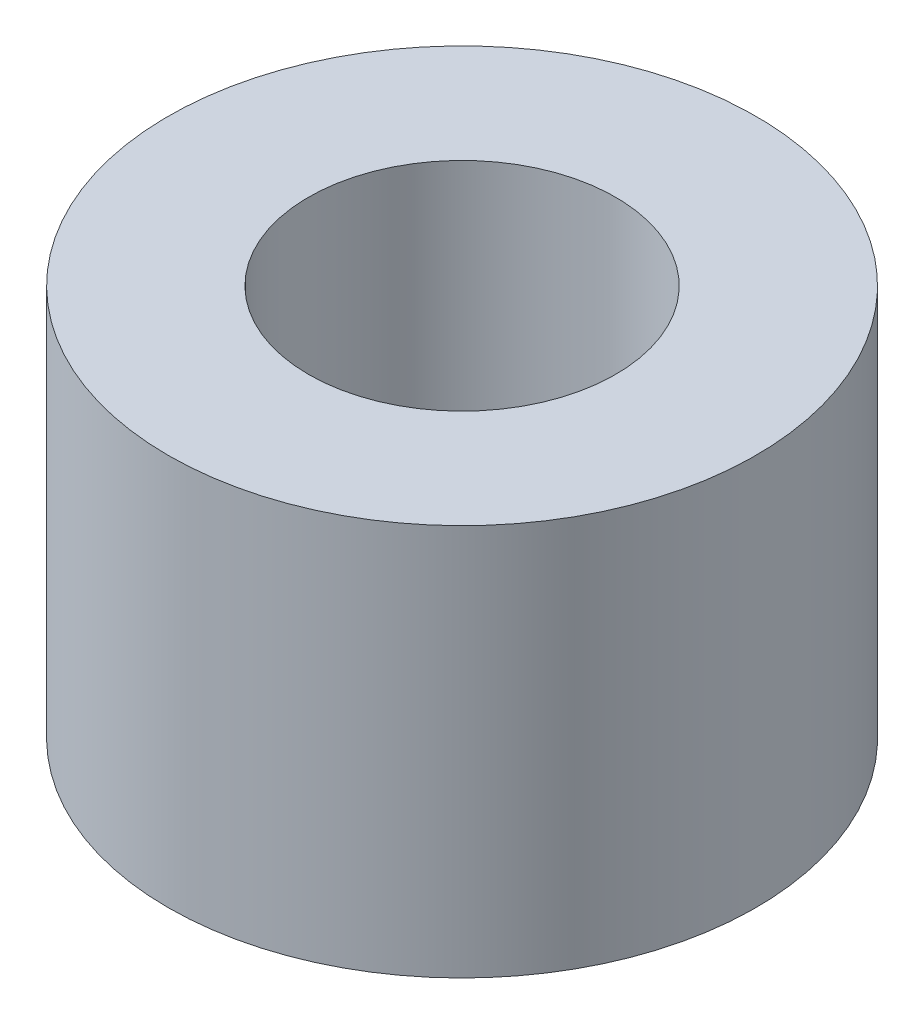
SolidWorks part; units mm, degrees
material "6061 Alloy"
ref_plane "Front Plane" through (0, 0, 0) normal (0, 0, 1) x (1, 0, 0)
ref_plane "Top Plane" through (0, 0, 0) normal (0, 1, 0) x (1, 0, 0)
ref_plane "Right Plane" through (0, 0, 0) normal (1, 0, 0) x (0, 0, -1)
sketch "Sketch1" plane through (0, 0, 0) normal (0, 1, 0) x (1, 0, 0)
  circle A0 centre (0, 0) radius 2.4892
  circle A1 centre (0, 0) radius 4.7625
  dimension "D1" = 4.9784
  dimension "D2" = 9.525
extrude "Boss-Extrude1" add sketch "Sketch1" along normal blind 6.35
